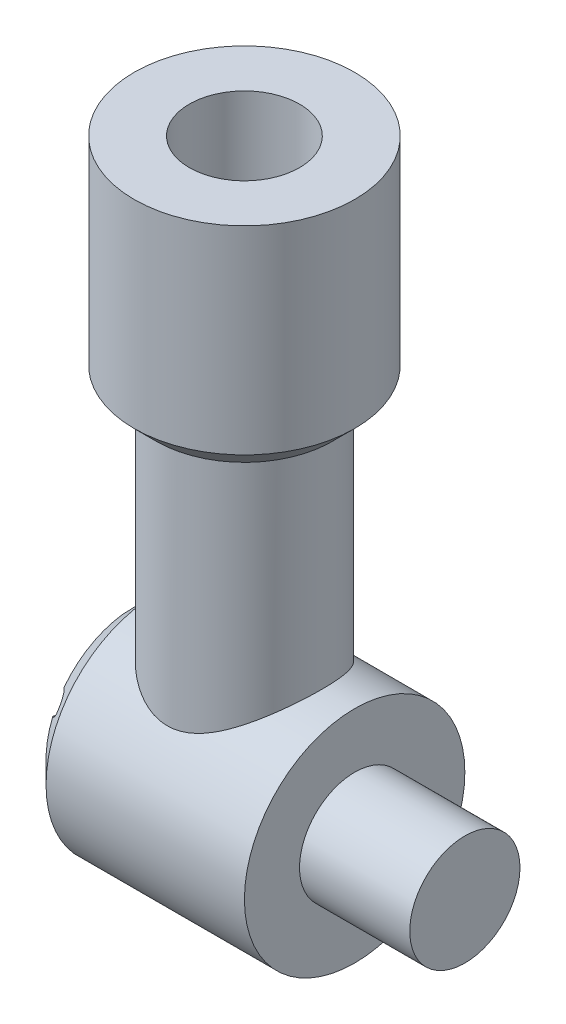
SolidWorks part; units mm, degrees
ref_plane "Front Plane" through (0, 0, 0) normal (0, 0, 1) x (1, 0, 0)
ref_plane "Top Plane" through (0, 0, 0) normal (0, 1, 0) x (1, 0, 0)
ref_plane "Right Plane" through (0, 0, 0) normal (1, 0, 0) x (0, 0, -1)
sketch "Sketch1" plane through (0, 0, 0) normal (0, 1, 0) x (1, 0, 0)
  circle A0 centre (0, 0) radius 88.9
  dimension "D1" = 177.8
extrude "Boss-Extrude1" add sketch "Sketch1" along normal mid plane 304.8
sketch "Sketch4" plane through (0, 0, 0) normal (1, 0, 0) x (0, 0, -1)
  line L2 (0, -152.4) -> (0, -304.8)
  line L3 (-88.9, -152.4) -> (88.9, -152.4) construction
  circle A1 centre (0, -228.6) radius 127
  dimension "D4" = 254
  dimension "D3" = 152.4
extrude "Boss-Extrude2" add sketch "Sketch4" along normal mid plane 254
sketch "Sketch5" plane through (127, 0, 0) normal (1, 0, 0) x (0, 0, -1)
  circle A0 centre (0, -228.6) radius 63.5
  circle A1 centre (0, -228.6) radius 127 construction
  dimension "D2" = 127
  dimension "D1" = 63.5
extrude "Boss-Extrude3" add sketch "Sketch5" along normal blind 127
sketch "Sketch6" plane through (0, 152.4, 0) normal (0, 1, 0) x (1, 0, 0)
  circle A0 centre (0, 0) radius 127
  circle A1 centre (0, 0) radius 88.9 construction
  dimension "D2" = 254
  dimension "D1" = 38.1
extrude "Boss-Extrude4" add sketch "Sketch6" along normal blind 254
sketch "Sketch7" plane through (0, 406.4, 0) normal (0, 1, 0) x (1, 0, 0)
  circle A0 centre (0, 0) radius 63.5
  circle A1 centre (0, 0) radius 127 construction
  dimension "D2" = 127
  dimension "D1" = 63.5
extrude "Cut-Extrude1" cut sketch "Sketch7" against normal blind 127
chamfer "Chamfer1" distance 25.4 angle 45 1 edges at (-127, -228.6, -127)
sketch "Sketch8" plane through (-127, 0, 0) normal (-1, 0, 0) x (0, 0, 1)
  circle A0 centre (0, -127) radius 12.7
  circle A1 centre (0, -228.6) radius 101.6 construction
  circle A2 centre (87.9882, -177.8) radius 12.7
  circle A3 centre (87.9882, -279.4) radius 12.7
  circle A4 centre (0, -330.2) radius 12.7
  circle A5 centre (-87.9882, -279.4) radius 12.7
  circle A6 centre (-87.9882, -177.8) radius 12.7
  point P16 (0, -228.6)
  dimension "D1" = 25.4
  dimension "D2" = 6
extrude "Cut-Extrude2" cut sketch "Sketch8" against normal blind 25.4
chamfer "Chamfer2" distance 25.4 angle 45 1 edges at (0, 152.4, 127)
